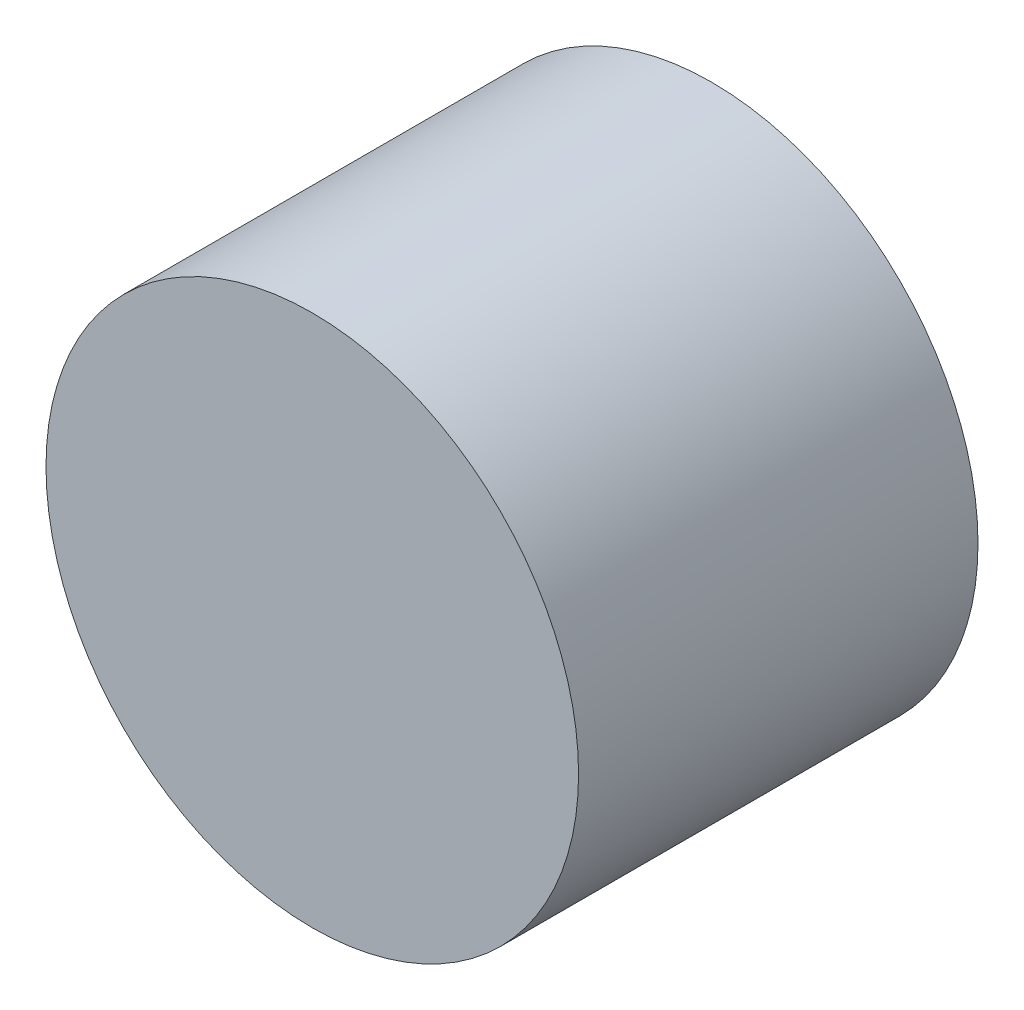
SolidWorks part; units mm, degrees
ref_plane "Alzado" through (0, 0, 0) normal (0, 0, 1) x (1, 0, 0)
ref_plane "Planta" through (0, 0, 0) normal (0, 1, 0) x (1, 0, 0)
ref_plane "Vista lateral" through (0, 0, 0) normal (1, 0, 0) x (0, 0, -1)
sketch "Croquis1" plane through (0, 0, 0) normal (0, 0, 1) x (1, 0, 0)
  circle A0 centre (0, 0) radius 10
  dimension "D1" = 20
extrude "Saliente-Extruir1" add sketch "Croquis1" along normal blind 15
